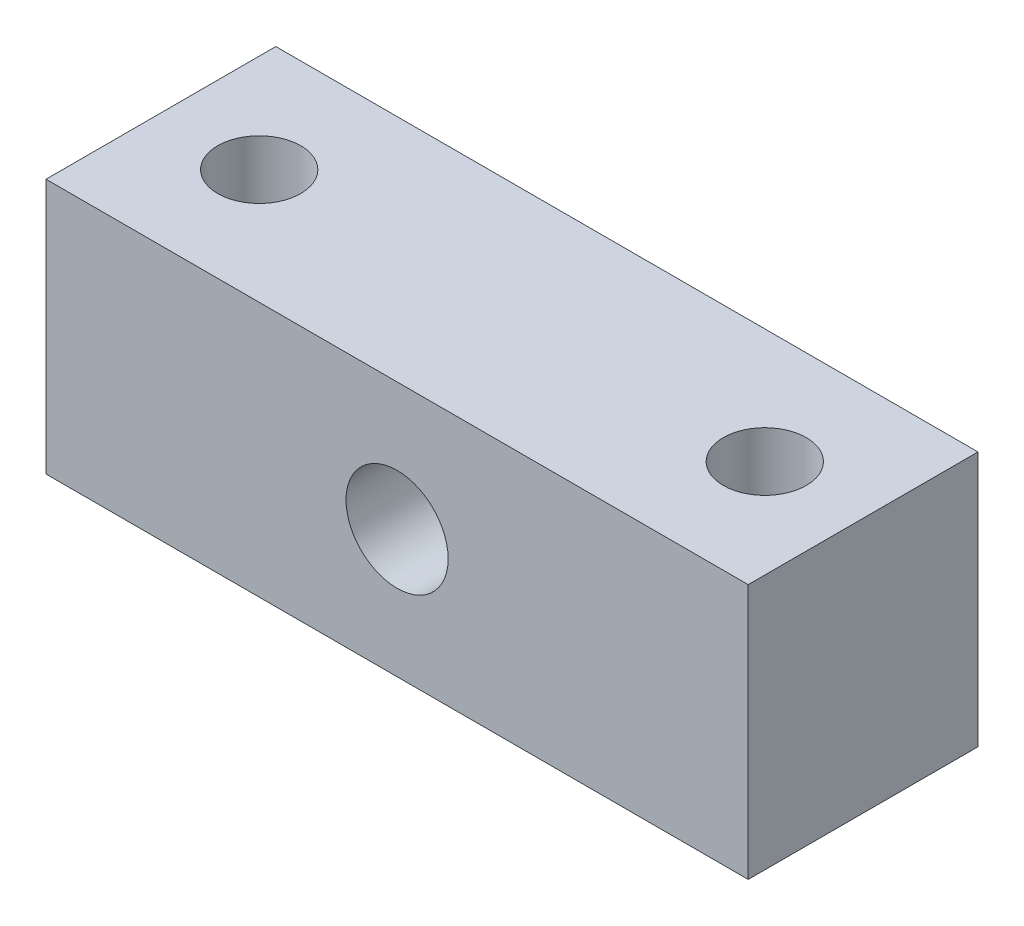
SolidWorks part; units mm, degrees
ref_plane "Спереди" through (0, 0, 0) normal (0, 0, 1) x (1, 0, 0)
ref_plane "Сверху" through (0, 0, 0) normal (0, 1, 0) x (1, 0, 0)
ref_plane "Справа" through (0, 0, 0) normal (1, 0, 0) x (0, 0, -1)
sketch "Эскиз1" plane through (0, 0, 0) normal (0, 0, 1) x (1, 0, 0)
  line L1 (-27.5, -10) -> (27.5, -10)
  line L2 (-27.5, -10) -> (-27.5, 10)
  line L3 (-27.5, 10) -> (27.5, 10)
  line L4 (27.5, -10) -> (27.5, 10)
  line L5 (-27.5, -10) -> (27.5, 10) construction
  line L6 (-27.5, 10) -> (27.5, -10) construction
  point P0 (0, 0)
  dimension "D1" = 55
  dimension "D2" = 20
extrude "Бобышка-Вытянуть1" add sketch "Эскиз1" along normal blind 18
sketch "Эскиз2" plane through (0, 0, 18) normal (0, 0, 1) x (1, 0, 0)
  circle A0 centre (0, 0) radius 4
  dimension "D1" = 8
extrude "Вырез-Вытянуть1" cut sketch "Эскиз2" against normal blind 18
hole_wizard "Диаметр отверстия Ø6.5 (6.5)1" positions "Эскиз3" profile "Эскиз4" hole size "Ø6.5" standard "DIN" end condition through all
sketch "Эскиз3" plane through (0, 10, 0) normal (0, 1, 0) x (1, 0, 0)
  line L0 (27.5, 0) -> (-27.5, 0) construction
  point P0 (19.8, -9)
  point P2 (-19.8, -9)
  point P5 (14.3115, -8.5478)
  point P9 (0, 0)
  dimension "D1" = 9
  dimension "D2" = 19.8
  dimension "D3" = 39.6
sketch "Эскиз4" plane through (19.8, 10, 9) normal (1, 0, 0) x (0, 0, 1)
  line L0 (0, 0) -> (0, 20)
  line L1 (0, 20) -> (3.25, 20)
  line L2 (3.25, 20) -> (3.25, 0)
  line L5 (3.25, 0) -> (0, 0)
  line L11 (0, -6.35) -> (0, 107.95) construction
  dimension "Диаметр сквозного отверстия" = 6.5
  dimension "Глубина сквозного отверстия" = 20
